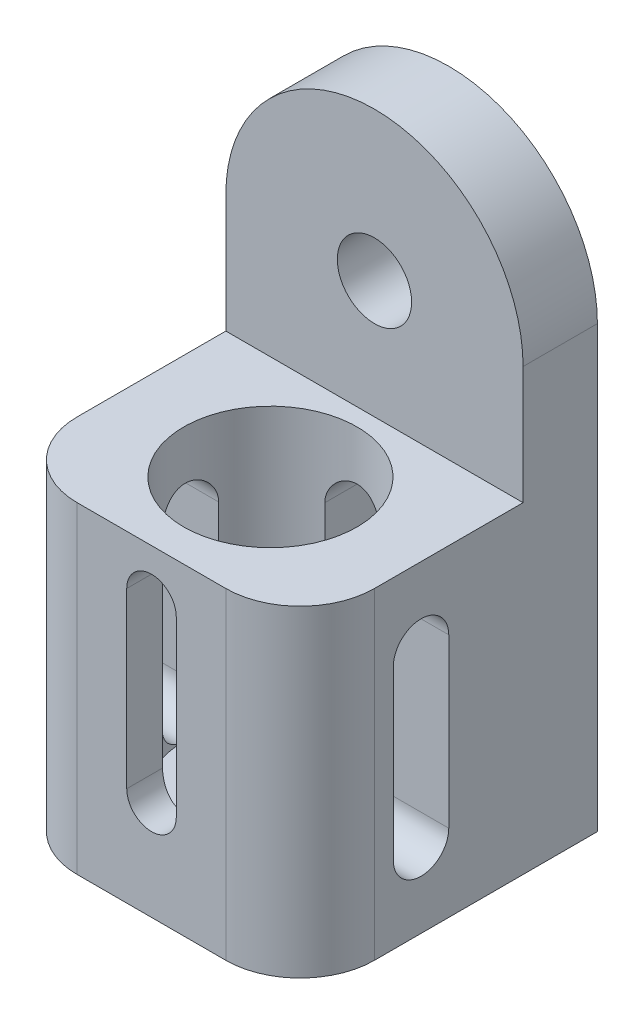
SolidWorks part; units mm, degrees
material "6061-T6 (SS)"
ref_plane "Front" through (0, 0, 0) normal (0, 0, 1) x (1, 0, 0)
ref_plane "Top" through (0, 0, 0) normal (0, 1, 0) x (1, 0, 0)
ref_plane "Right" through (0, 0, 0) normal (1, 0, 0) x (0, 0, -1)
sketch "Sketch1" plane through (0, 0, 0) normal (0, 1, 0) x (1, 0, 0)
  line L1 (-19.05, -38.1) -> (19.05, -38.1)
  line L2 (-38.1, -19.05) -> (-38.1, 38.1)
  line L3 (-38.1, 38.1) -> (38.1, 38.1)
  line L4 (38.1, -19.05) -> (38.1, 38.1)
  line L5 (-38.1, -38.1) -> (38.1, 38.1) construction
  line L6 (-38.1, 38.1) -> (38.1, -38.1) construction
  arc A0 (19.05, -38.1) -> (38.1, -19.05) centre (19.05, -19.05) ccw
  arc A1 (-19.05, -38.1) -> (-38.1, -19.05) centre (-19.05, -19.05) cw
  point P0 (0, 0)
  dimension "D2" = 19.05
  dimension "D1" = 76.2
  dimension "D3" = 76.2
extrude "Boss-Extrude1" add sketch "Sketch1" along normal blind 150.876
sketch "Sketch2" plane through (0, 0, 38.1) normal (0, 0, 1) x (1, 0, 0)
  line L0 (-38.1, 150.876) -> (-38.1, 0) construction
  line L1 (38.1, 150.876) -> (38.1, 0) construction
  line L2 (-19.05, 150.876) -> (19.05, 150.876) construction
  line L3 (-38.1, 112.776) -> (-38.1, 150.876)
  line L4 (-38.1, 150.876) -> (38.1, 150.876)
  line L5 (38.1, 150.876) -> (38.1, 112.776)
  arc A0 (-38.1, 112.776) -> (38.1, 112.776) centre (0, 112.776) cw
  line M2 (19.05, 0) -> (19.05, 150.876)
  line M3 (19.05, 150.876) -> (-19.05, 150.876)
  line M4 (-19.05, 150.876) -> (-19.05, 0)
extrude "Cut-Extrude1" cut sketch "Sketch2" against normal through all contours A0 L5 L4 M2 | A0 M3 M2 | A0 L4 M4 | L3 A0 L4 M4
sketch "Sketch3" plane through (38.1, 0, 0) normal (1, 0, 0) x (0, 0, -1)
  line L0 (-38.1, 150.876) -> (-38.1, 145.7716) construction
  line L1 (-38.1, 150.876) -> (19.05, 150.876)
  line L2 (-38.1, 150.876) -> (-38.1, 82.55)
  line L3 (-38.1, 82.55) -> (19.05, 82.55)
  line L4 (19.05, 150.876) -> (19.05, 82.55)
  line L5 (-38.1, 145.7716) -> (-38.1, 0) construction
  line L6 (38.1, 112.776) -> (38.1, 0) construction
  line L7 (-19.05, 0) -> (38.1, 0) construction
  dimension "D1" = 19.05
  dimension "D2" = 82.55
extrude "Cut-Extrude2" cut sketch "Sketch3" against normal through all
hole_wizard "3/4 (0.75) Diameter Hole1" positions "Sketch4" profile "Sketch5" hole size "3/4" standard "ANSI Inch" end condition through all
sketch "Sketch4" plane through (0, 0, -19.05) normal (0, 0, 1) x (1, 0, 0)
  point P0 (0, 112.776)
sketch "Sketch5" plane through (0, 112.776, -19.05) normal (1, 0, 0) x (0, -1, 0)
  line L0 (0, 0) -> (0, 19.05)
  line L1 (0, 19.05) -> (9.525, 19.05)
  line L2 (9.525, 19.05) -> (9.525, 0)
  line L5 (9.525, 0) -> (0, 0)
  line L11 (0, -6.35) -> (0, 107.95) construction
  dimension "Thru Hole Dia." = 19.05
  dimension "Thru Hole Depth" = 19.05
sketch "Sketch6" plane through (0, 82.55, 0) normal (0, 1, 0) x (1, 0, 0)
  line L0 (-19.05, -38.1) -> (19.05, -38.1) construction
  line L1 (0, -7.62) -> (0, 0) construction
  circle A0 centre (0, -7.62) radius 22.225
  dimension "D2" = 44.45
  dimension "D1" = 30.48
extrude "Cut-Extrude3" cut sketch "Sketch6" against normal blind 69.85
sketch "Sketch7" plane through (0, 0, 38.1) normal (0, 0, 1) x (1, 0, 0)
  line L0 (0, 25.4) -> (0, 69.85) construction
  line L1 (-6.35, 25.4) -> (-6.35, 69.85)
  line L2 (6.35, 25.4) -> (6.35, 69.85)
  line L3 (-19.05, 0) -> (19.05, 0) construction
  arc A0 (-6.35, 25.4) -> (6.35, 25.4) centre (0, 25.4) ccw
  arc A1 (6.35, 69.85) -> (-6.35, 69.85) centre (0, 69.85) ccw
  point P3 (0, 47.625)
  dimension "D1" = 12.7
  dimension "D2" = 44.45
  dimension "D3" = 25.4
extrude "Cut-Extrude4" cut sketch "Sketch7" against normal up to surface (9.1815 mm away)
sketch "Sketch8" plane through (38.1, 0, 0) normal (1, 0, 0) x (0, 0, -1)
  line L0 (-7.112, 62.738) -> (-7.112, 19.812) construction
  line L1 (0, 62.738) -> (0, 19.812)
  line L2 (-14.224, 62.738) -> (-14.224, 19.812)
  line L3 (-38.1, 82.55) -> (-38.1, 0) construction
  line L4 (-19.05, 0) -> (38.1, 0) construction
  arc A0 (0, 62.738) -> (-14.224, 62.738) centre (-7.112, 62.738) ccw
  arc A1 (-14.224, 19.812) -> (0, 19.812) centre (-7.112, 19.812) ccw
  point P2 (-7.112, 41.275)
  dimension "D1" = 30.988
  dimension "D2" = 14.224
  dimension "D3" = 42.926
  dimension "D4" = 19.812
extrude "Cut-Extrude5" cut sketch "Sketch8" against normal up to surface (17.2221 mm away)
mirror "Mirror1" about plane through (0, 0, 0) normal (1, 0, 0) of "Cut-Extrude5"
sketch "Sketch9" plane through (0, 0, -38.1) normal (0, 0, -1) x (-1, 0, 0)
  line L0 (0, 19.812) -> (0, 62.738) construction
  line L1 (-7.112, 19.812) -> (-7.112, 62.738)
  line L2 (7.112, 19.812) -> (7.112, 62.738)
  line L3 (-38.1, 0) -> (38.1, 0) construction
  arc A0 (-7.112, 19.812) -> (7.112, 19.812) centre (0, 19.812) ccw
  arc A1 (7.112, 62.738) -> (-7.112, 62.738) centre (0, 62.738) ccw
  point P3 (0, 41.275)
  dimension "D1" = 14.224
  dimension "D2" = 42.926
  dimension "D3" = 19.812
extrude "Cut-Extrude6" cut sketch "Sketch9" against normal up to surface (24.6636 mm away)
